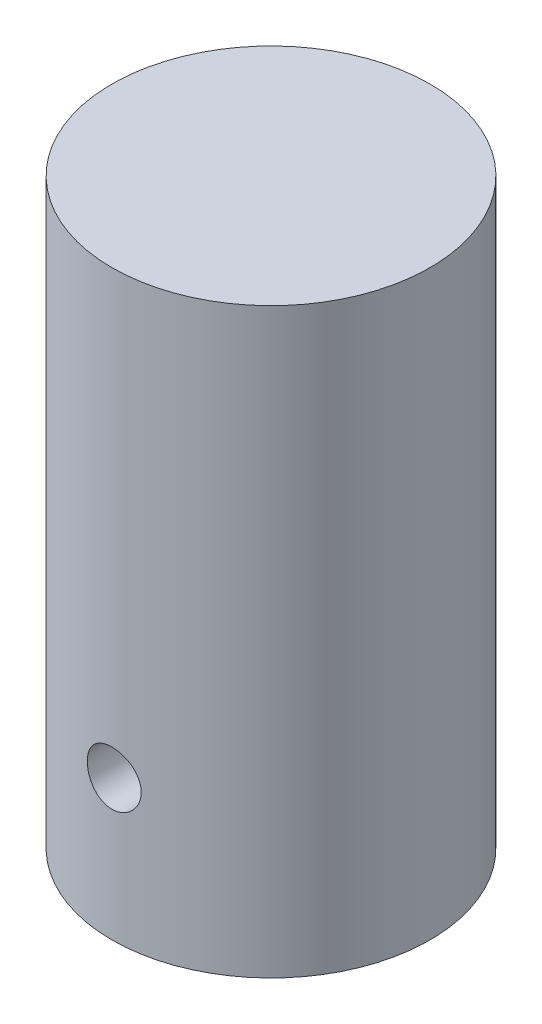
SolidWorks part; units mm, degrees
ref_plane "Front Plane" through (0, 0, 0) normal (0, 0, 1) x (1, 0, 0)
ref_plane "Top Plane" through (0, 0, 0) normal (0, 1, 0) x (1, 0, 0)
ref_plane "Right Plane" through (0, 0, 0) normal (1, 0, 0) x (0, 0, -1)
sketch "Sketch1" plane through (0, 0, 0) normal (0, 1, 0) x (1, 0, 0)
  circle A0 centre (0, 0) radius 37.465
  dimension "D1" = 74.93
extrude "Boss-Extrude1" add sketch "Sketch1" along normal blind 137.16
ref_plane "Plane1" through (0, 0, 37.465) normal (0, 0, 1) x (1, 0, 0)
sketch "Sketch3" plane through (0, 0, 37.465) normal (0, 0, 1) x (1, 0, 0)
  line L0 (0, 0) -> (0, 33.02) construction
  circle A0 centre (0, 33.02) radius 6.35
  dimension "D2" = 12.7
  dimension "D1" = 33.02
extrude "Cut-Extrude1" cut sketch "Sketch3" against normal blind 19.05
sketch "Sketch4" plane through (0, 0, 0) normal (0, -1, 0) x (1, 0, 0)
  circle A0 centre (0, 0) radius 6.35
  dimension "D1" = 12.7
extrude "Cut-Extrude2" cut sketch "Sketch4" against normal blind 19.05
